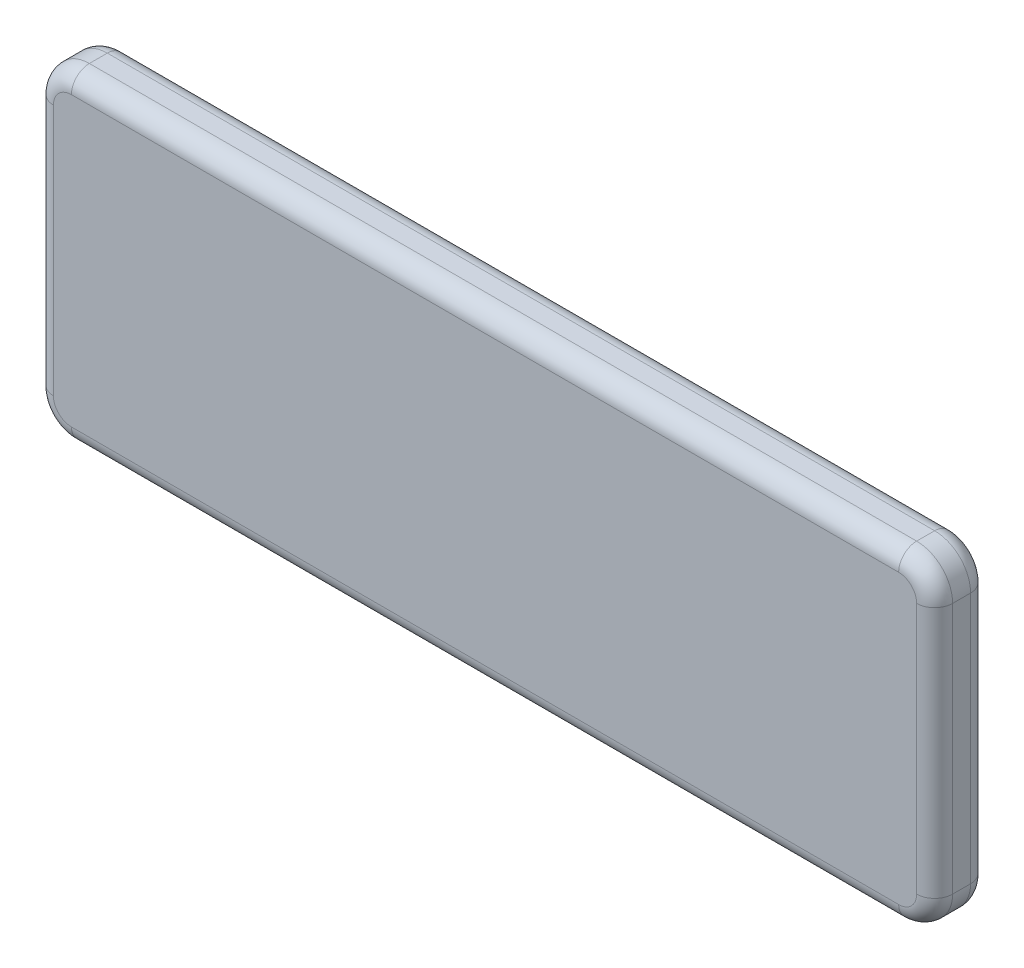
SolidWorks part; units mm, degrees
ref_plane "Front Plane" through (0, 0, 0) normal (0, 0, 1) x (1, 0, 0)
ref_plane "Top Plane" through (0, 0, 0) normal (0, 1, 0) x (1, 0, 0)
ref_plane "Right Plane" through (0, 0, 0) normal (1, 0, 0) x (0, 0, -1)
sketch "Sketch1" plane through (0, 0, 0) normal (0, 0, 1) x (1, 0, 0)
  line L1 (-125, 45) -> (125, 45)
  line L2 (-125, 45) -> (-125, -45)
  line L3 (-125, -45) -> (125, -45)
  line L4 (125, 45) -> (125, -45)
  line L5 (-125, 45) -> (125, -45) construction
  line L6 (-125, -45) -> (125, 45) construction
  point P0 (0, 0)
  dimension "D1" = 250
  dimension "D2" = 90
extrude "Boss-Extrude1" add sketch "Sketch1" along normal blind 15
fillet "Fillet1" radius 10 4 edges at (125, 45, 7.5) (125, -45, 7.5) (-125, -45, 7.5) (-125, 45, 7.5)
fillet "Fillet2" radius 5 16 edges at (122.0711, 42.0711, 15) (125, 0, 15) (122.0711, -42.0711, 15) (0, -45, 15) (-122.0711, -42.0711, 15) (-125, 0, 15) (-122.0711, 42.0711, 15) (122.0711, 42.0711, 0) (125, 0, 0) (122.0711, -42.0711, 0) (0, -45, 0) (-122.0711, -42.0711, 0) (-125, 0, 0) (-122.0711, 42.0711, 0) (0, 45, 15) (0, 45, 0)
